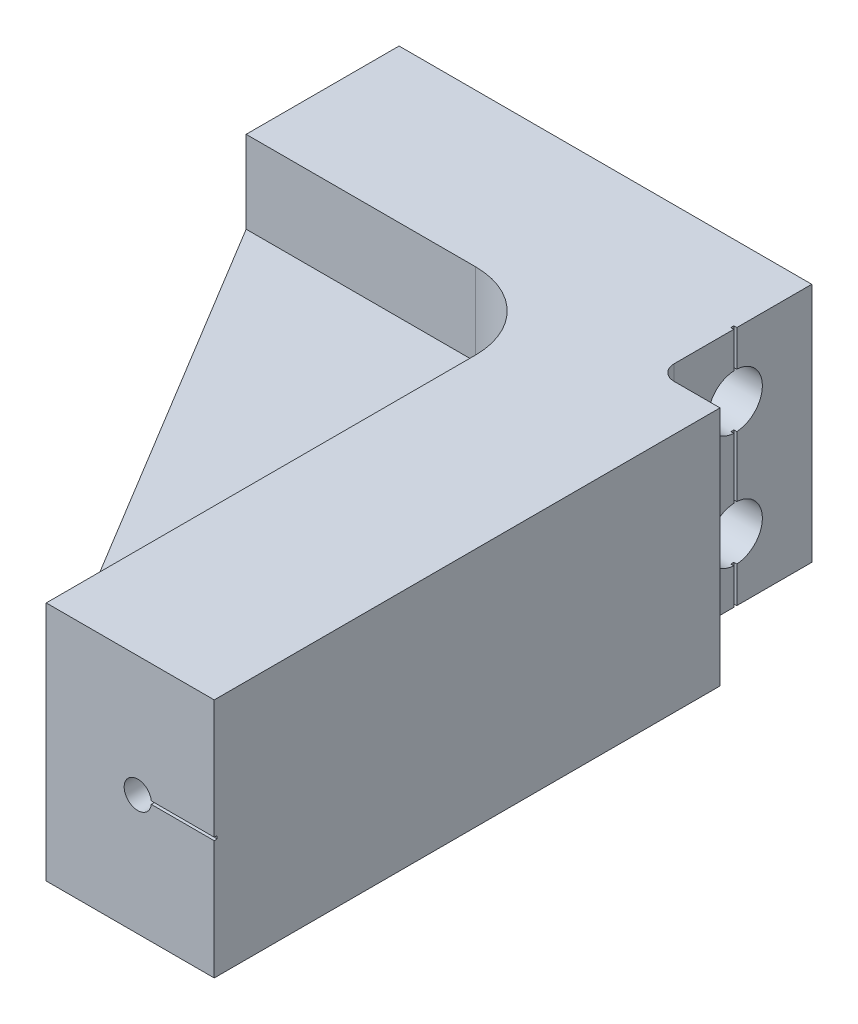
SolidWorks part; units mm, degrees
ref_plane "Front" through (0, 0, 0) normal (0, 0, 1) x (1, 0, 0)
ref_plane "Top" through (0, 0, 0) normal (0, 1, 0) x (1, 0, 0)
ref_plane "Right" through (0, 0, 0) normal (1, 0, 0) x (0, 0, -1)
sketch "Sketch1" plane through (0, 0, 0) normal (0, 0, 1) x (1, 0, 0)
  line L0 (0, 10) -> (0, -10)
  line L4 (-6.7379, 0) -> (17.2192, 0) construction
  line L5 (0, 10) -> (24.25, 10)
  line L7 (0, -10) -> (24.25, -10)
  line L8 (24.25, 10) -> (24.25, -10)
  dimension "D1" = 24.25
  dimension "D3" = 20
extrude "Extrude1" add sketch "Sketch1" along normal blind 54.7
sketch "Sketch4" plane through (0, -10, 0) normal (0, -1, 0) x (1, 0, 0)
  line L0 (0, 12.7) -> (3.95, 12.7)
  line L1 (0, 54.7) -> (10.3, 54.7)
  line L2 (0, 54.7) -> (0, 12.7)
  line L4 (10.3, 54.7) -> (10.3, 19.05)
  arc A0 (3.95, 12.7) -> (10.3, 19.05) centre (3.95, 19.05) ccw
  dimension "D1" = 6.35
  dimension "D2" = 10.3
  dimension "D3" = 12.7
extrude "Cut-Extrude1" cut sketch "Sketch4" against normal through all
sketch "Sketch5" plane through (0, 0, 0) normal (-1, 0, 0) x (0, 0, 1)
  line L1 (0, -10) -> (12.7, -10)
  line L2 (0, -10) -> (0, 10)
  line L3 (0, 10) -> (12.7, 10)
  line L4 (12.7, -10) -> (12.7, 10)
extrude "Extrude2" add sketch "Sketch5" along normal blind 15.1
hole_wizard "#8 Clearance Hole1" positions "Sketch7" profile "Sketch6" hole size "#8" standard "Ansi Inch" end condition through all
sketch "Sketch7" plane through (24.25, 0, 0) normal (1, 0, 0) x (0, 0, -1)
  line L0 (2.7308, 0) -> (-7.5588, 0) construction
  line L1 (0, -10) -> (0, 10) construction
  point P0 (-6.35, 4.7625)
  point P1 (-6.35, -4.7625)
  dimension "D1" = 6.35
  dimension "D2" = 9.525
sketch "Sketch6" plane through (24.25, 4.7625, 6.35) normal (0, 1, 0) x (0, 0, -1)
  line L0 (0, 0) -> (0, 39.35)
  line L1 (0, 39.35) -> (2.2479, 39.35)
  line L2 (2.2479, 39.35) -> (2.2479, 0)
  line L5 (2.2479, 0) -> (0, 0)
  line L11 (0, -6.35) -> (0, 107.95) construction
  dimension "Thru Hole Dia." = 4.4958
  dimension "Thru Hole Depth" = 39.35
hole_wizard "#4-40 Tapped Hole1" positions "Sketch10" profile "Sketch9" tap size "#4-40" standard "Ansi Inch"
sketch "Sketch10" plane through (0, 0, 54.7) normal (0, 0, 1) x (1, 0, 0)
  line L0 (24.25, -10) -> (24.25, 10) construction
  line L1 (0, 0) -> (24.25, 0) construction
  point P0 (17.9, 0)
  dimension "D1" = 6.35
cosmetic thread "Cosmetic Thread1" parameters "D1"=5.6896, "D2"=2.8448
sketch "Sketch9" plane through (17.9, 0, 54.7) normal (1, 0, 0) x (0, -1, 0)
  line L0 (0, 0) -> (0, 9.5438)
  line L1 (0, 9.5438) -> (1.1303, 8.8646)
  line L2 (1.1303, 8.8646) -> (1.1303, 0)
  line L5 (1.1303, 0) -> (0, 0)
  line L10 (0, 9.5438) -> (-1.1303, 8.8646) construction
  line L11 (0, -6.35) -> (0, 107.95) construction
  dimension "Tap Drill Dia." = 2.2606
  dimension "Tap Drill Depth" = 8.8646
  dimension "Drill Angle" = 118
sketch "Sketch11" plane through (24.25, 0, 0) normal (1, 0, 0) x (0, 0, -1)
  line L0 (-54.7, 10) -> (0, 10) construction
  line L1 (-12.7, 10) -> (0, 10)
  line L2 (-12.7, 10) -> (-12.7, -10)
  line L3 (-12.7, -10) -> (0, -10)
  line L4 (0, 10) -> (0, -10)
  line L5 (-54.7, -10) -> (0, -10) construction
  dimension "D1" = 12.7
extrude "Cut-Extrude2" cut sketch "Sketch11" against normal blind 5.08
fillet "Fillet1" radius 1.27 1 edges at (19.17, 0, 12.7)
sketch "Sketch12" plane through (19.17, 0, 0) normal (1, 0, 0) x (0, 0, -1)
  line L0 (0, 10) -> (-11.43, 10) construction
  line L1 (-6.475, 10) -> (-6.225, 10)
  line L2 (-6.475, 10) -> (-6.475, -10)
  line L3 (-6.475, -10) -> (-6.225, -10)
  line L4 (-6.225, 10) -> (-6.225, -10)
  line L5 (-11.43, -10) -> (0, -10) construction
  line L6 (-6.35, 4.7625) -> (-6.35, -4.7625) construction
  dimension "D1" = 0.25
extrude "Cut-Extrude3" cut sketch "Sketch12" against normal blind 0.25
sketch "Sketch13" plane through (0, 0, 0) normal (0, 1, 0) x (1, 0, 0)
  line L0 (-15.1, -12.7) -> (10.3, -54.7)
  line L1 (10.3, -54.7) -> (10.3, -12.7)
  line L2 (10.3, -12.7) -> (-15.1, -12.7)
extrude "Extrude3" add sketch "Sketch13" along normal mid plane 6.35
sketch "Sketch14" plane through (0, 0, 54.7) normal (0, 0, 1) x (1, 0, 0)
  line L0 (24.25, -10) -> (24.25, 10) construction
  line L1 (24.25, 0.125) -> (17.9, 0.125)
  line L2 (24.25, 0.125) -> (24.25, -0.125)
  line L3 (24.25, -0.125) -> (17.9, -0.125)
  line L4 (17.9, 0.125) -> (17.9, -0.125)
  line L5 (-2.0764, 0) -> (2.0168, 0) construction
  dimension "D1" = 0.25
extrude "Cut-Extrude4" cut sketch "Sketch14" against normal blind 0.25
